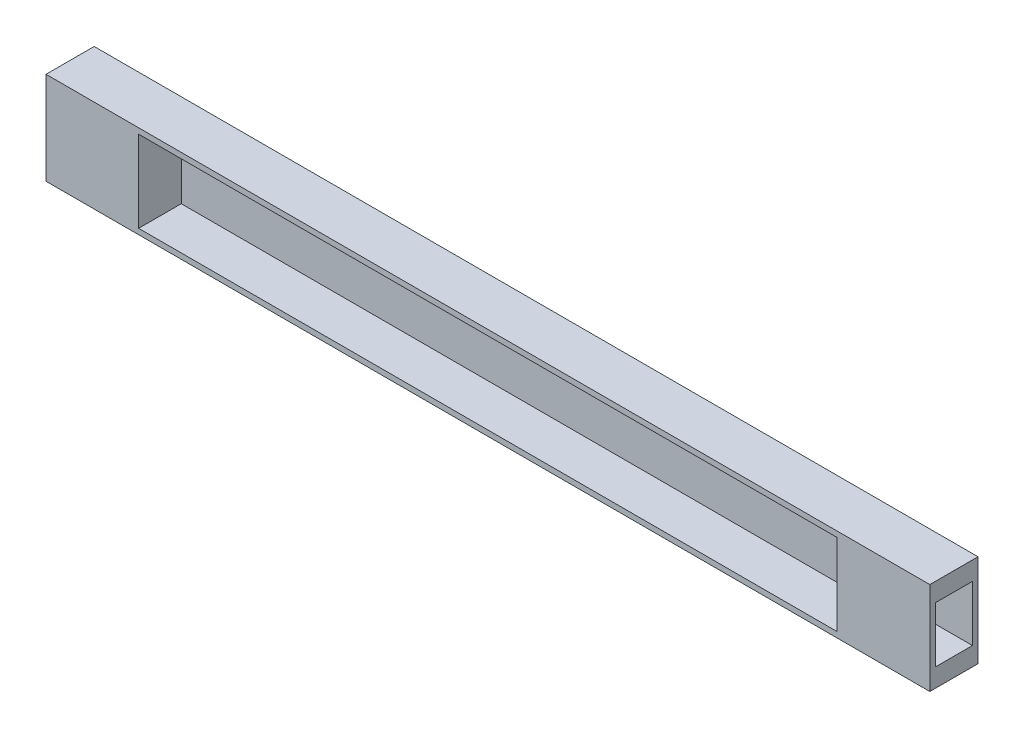
SolidWorks part; units mm, degrees
ref_plane "Front Plane" through (0, 0, 0) normal (0, 0, 1) x (1, 0, 0)
ref_plane "Top Plane" through (0, 0, 0) normal (0, 1, 0) x (1, 0, 0)
ref_plane "Right Plane" through (0, 0, 0) normal (1, 0, 0) x (0, 0, -1)
ref_plane "Plane1" through (0, 0, 514) normal (0, 0, 1) x (1, 0, 0)
sketch "Sketch1" plane through (0, 0, 514) normal (0, 0, 1) x (1, 0, 0)
  line L0 (-61, 170) -> (-61, 120)
  line L1 (-61, 120) -> (416, 120)
  line L2 (416, 120) -> (416, 170)
  line L3 (416, 170) -> (-61, 170)
extrude "Boss-Extrude1" add sketch "Sketch1" against normal blind 26
sketch "Sketch2" plane through (-61, 0, 0) normal (-1, 0, 0) x (0, 0, 1)
  line L0 (514, 167) -> (491, 167)
  line L1 (491, 167) -> (491, 123)
  line L2 (491, 123) -> (514, 123)
  line L3 (514, 123) -> (514, 167)
extrude "Cut-Extrude1" cut sketch "Sketch2" against normal blind 427
sketch "Sketch3" plane through (416, 0, 0) normal (1, 0, 0) x (0, 0, -1)
  line L0 (-511, 130) -> (-491, 130)
  line L1 (-491, 130) -> (-491, 160)
  line L2 (-491, 160) -> (-511, 160)
  line L3 (-511, 160) -> (-511, 130)
extrude "Cut-Extrude2" cut sketch "Sketch3" against normal blind 30
other "Move Face1" face at (-61, 145, 501.75) parameters "D1"=238.5
other "Move Face2" face at (386, 145, 501) parameters "D1"=30
sketch "Sketch6" plane through (416, 0, 0) normal (1, 0, 0) x (0, 0, -1)
  line L7 (-511, 130) -> (-491, 130)
  line L8 (-511, 130) -> (-511, 160)
  line L9 (-511, 160) -> (-491, 160)
  line L10 (-491, 130) -> (-491, 160)
  point P12 (-501, 145)
extrude "Cut-Extrude3" cut sketch "Sketch6" against normal blind 30 contours L8 L7 L10 L9
mirror "Mirror3" about plane through (177.5, 170, 488) normal (-1, 0, 0) of bodies 109
sketch "Sketch7" plane through (0, 0, 488) normal (0, 0, -1) x (-1, 0, 0)
  line L0 (-177.5, 170) -> (-177.5, 120) construction
  line L1 (-416, 170) -> (61, 170) construction
  line L2 (61, 120) -> (-416, 120) construction
  line L3 (-416, 145) -> (61, 145) construction
  line L4 (-416, 120) -> (-416, 170) construction
  line L5 (61, 120) -> (61, 170) construction
  line L11 (-187.5, 135) -> (-167.5, 135)
  line L12 (-187.5, 135) -> (-187.5, 155)
  line L13 (-187.5, 155) -> (-167.5, 155)
  line L14 (-167.5, 135) -> (-167.5, 155)
  line L15 (-187.5, 135) -> (-167.5, 155) construction
  line L16 (-187.5, 155) -> (-167.5, 135) construction
  point P12 (-177.5, 145)
  point P13 (-177.5, 145)
  dimension "D1" = 20
  dimension "D2" = 20
extrude "Boss-Extrude3" add sketch "Sketch7" along normal blind 10 contours L12 L11 L14 L13
